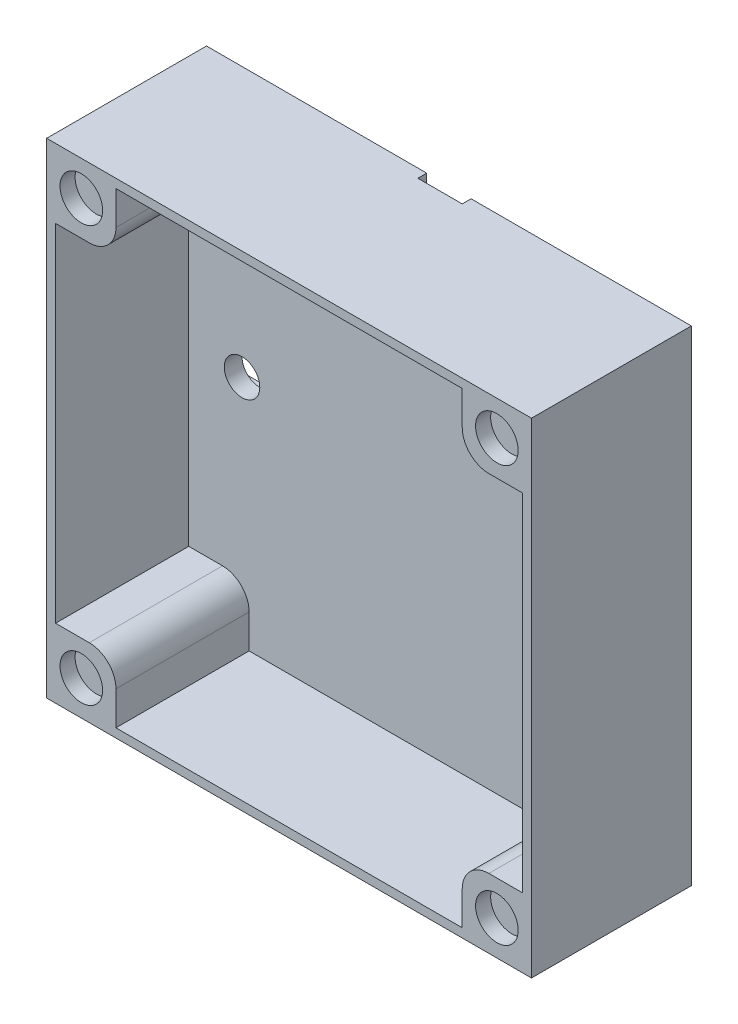
SolidWorks part; units mm, degrees
ref_plane "Přední rovina" through (0, 0, 0) normal (0, 0, 1) x (1, 0, 0)
ref_plane "Horní rovina" through (0, 0, 0) normal (0, 1, 0) x (1, 0, 0)
ref_plane "Pravá rovina" through (0, 0, 0) normal (1, 0, 0) x (0, 0, -1)
sketch "Skica1" plane through (0, 0, 0) normal (0, 0, 1) x (1, 0, 0)
  line L1 (27.3, 27.3) -> (-27.3, 27.3)
  line L2 (27.3, 27.3) -> (27.3, -27.3)
  line L3 (27.3, -27.3) -> (-27.3, -27.3)
  line L4 (-27.3, 27.3) -> (-27.3, -27.3)
  line L5 (27.3, 27.3) -> (-27.3, -27.3) construction
  line L6 (27.3, -27.3) -> (-27.3, 27.3) construction
  point P0 (0, 0)
  point P5 (-27.5, 0)
  point P11 (4.5, 0)
  dimension "D1" = 54.6
  dimension "D2" = 54.6
extrude "Přidat vysunutím2" add sketch "Skica1" along normal blind 3 contours L2 L1 L4 L3
sketch "Skica5" plane through (0, 0, 0) normal (0, 0, -1) x (-1, 0, 0)
  line L0 (-27.3, 27.3) -> (27.3, 27.3) construction
  line L5 (2.5, 27.3) -> (-2.5, 27.3)
  line L15 (27.3, 27.3) -> (27.3, -27.3) construction
  line L16 (-2.5, 2.5) -> (27.3, 2.5)
  line L17 (2.5, 27.3) -> (2.5, 2.5)
  line L18 (2.5, 2.5) -> (-2.5, 2.5)
  line L19 (-2.5, 27.3) -> (-2.5, 2.5)
  line L20 (-27.3, 27.3) -> (-27.3, -27.3) construction
  line L21 (-2.5, 2.5) -> (-2.5, -2.5)
  line L22 (-2.5, -2.5) -> (27.3, -2.5)
  line L23 (27.3, 2.5) -> (27.3, -2.5)
  point P0 (0, 0)
  dimension "D1" = 5
  dimension "D2" = 24.8
  dimension "D3" = 5
  dimension "D4" = 24.8
extrude "Odebrat vysunutím3" cut sketch "Skica5" against normal blind 1 contours L23 L22 L21 L16 | L17 L5 L19 L18
sketch "Skica14" plane through (0, 0, 3) normal (0, 0, 1) x (1, 0, 0)
  line L1 (-27.3, 27.3) -> (27.3, 27.3)
  line L2 (-27.3, 27.3) -> (-27.3, -27.3)
  line L3 (-27.3, -27.3) -> (27.3, -27.3)
  line L4 (27.3, 27.3) -> (27.3, -27.3)
  line L5 (-26.3, 26.3) -> (26.3, 26.3)
  line L6 (-26.3, 26.3) -> (-26.3, -27.3)
  line L7 (-26.3, -27.3) -> (26.3, -27.3)
  line L8 (26.3, 26.3) -> (26.3, -27.3)
  line L9 (-26.3, -27.3) -> (26.3, -27.3)
  line L10 (-26.3, -27.3) -> (-26.3, -26.3)
  line L11 (-26.3, -26.3) -> (26.3, -26.3)
  line L12 (26.3, -27.3) -> (26.3, -26.3)
  line M13 (-27.3, -27.3) -> (27.3, -27.3)
  line M14 (27.3, -27.3) -> (27.3, 27.3)
  line M15 (27.3, 27.3) -> (-27.3, 27.3)
  line M16 (-27.3, 27.3) -> (-27.3, -27.3)
  dimension "D1" = 1
  dimension "D2" = 1
  dimension "D3" = 1
  dimension "D4" = 0
  dimension "D5" = 1
  dimension "D6" = 52.6
extrude "Přidat vysunutím9" add sketch "Skica14" along normal blind 15 contours L5 L8 L6 M13 M14 M15 M16 | L10 L9 L12 L11
sketch "Skica17" plane through (0, 0, 1) normal (0, 0, -1) x (-1, 0, 0)
  line L2 (27.3, 2.5) -> (27.3, -2.5) construction
  line L4 (2.5, 27.3) -> (-2.5, 27.3) construction
  circle A1 centre (20.3, 0) radius 2
  circle A2 centre (0, 20.3) radius 2
  dimension "D2" = 4
  dimension "D6" = 7
  dimension "D4" = 4
  dimension "D5" = 7
extrude "Odebrat vysunutím8" cut sketch "Skica17" against normal blind 7
sketch "Skica19" plane through (0, 0, 0) normal (0, 0, -1) x (-1, 0, 0)
  line L1 (-27.3, 27.3) -> (-19.5, 27.3)
  line L2 (-27.3, 27.3) -> (-27.3, 19.5)
  line L3 (-27.3, 19.5) -> (-19.5, 19.5)
  line L4 (-19.5, 27.3) -> (-19.5, 19.5)
  line L5 (27.3, 27.3) -> (19.5, 27.3)
  line L6 (27.3, 27.3) -> (27.3, 19.5)
  line L7 (27.3, 19.5) -> (19.5, 19.5)
  line L8 (19.5, 27.3) -> (19.5, 19.5)
  line L9 (-27.3, -27.3) -> (-19.5, -27.3)
  line L10 (-27.3, -27.3) -> (-27.3, -19.5)
  line L11 (-27.3, -19.5) -> (-19.5, -19.5)
  line L12 (-19.5, -27.3) -> (-19.5, -19.5)
  line L13 (27.3, -27.3) -> (19.5, -27.3)
  line L14 (27.3, -27.3) -> (27.3, -19.5)
  line L15 (27.3, -19.5) -> (19.5, -19.5)
  line L16 (19.5, -27.3) -> (19.5, -19.5)
  dimension "D1" = 7.8
  dimension "D2" = 7.8
  dimension "D3" = 7.8
  dimension "D4" = 7.8
extrude "Přidat vysunutím10" add sketch "Skica19" against normal blind 18
sketch "Skica20" plane through (0, 0, 18) normal (0, 0, 1) x (1, 0, 0)
  line L0 (-27.3, -27.3) -> (27.3, -27.3) construction
  line L1 (-19.5, -26.3) -> (-19.5, -19.5) construction
  line L2 (-27.3, 27.3) -> (-27.3, -27.3) construction
  line L3 (27.3, 27.3) -> (-27.3, 27.3) construction
  line L4 (27.3, -27.3) -> (27.3, 27.3) construction
  line L5 (-27.3, -27.3) -> (27.3, -27.3) construction
  circle A0 centre (-23.4, -23.4) radius 2.4
  circle A1 centre (-23.4, 23.4) radius 2.4
  circle A2 centre (23.4003, 23.4) radius 2.4
  circle A3 centre (23.4003, -23.4) radius 2.4
  dimension "D1" = 4.8
  dimension "D4" = 4.8
  dimension "D5" = 3.9
  dimension "D7" = 4.8
  dimension "D10" = 4.8
  dimension "D2" = 3.9
  dimension "D3" = 3.9
  dimension "D6" = 3.9
  dimension "D8" = 3.8997
  dimension "D9" = 3.9
  dimension "D11" = 3.9
  dimension "D12" = 3.8997
extrude "Odebrat vysunutím9" cut sketch "Skica20" against normal blind 1.7
fillet "Zaoblit1" radius 3 4 edges at (19.5, 19.5, 10.5) (19.5, -19.5, 10.5) (-19.5, -19.5, 10.5) (-19.5, 19.5, 10.5)
fillet "Zaoblit2" radius 15 1 edges at (-2.5, 2.5, 0.5)
fillet "Zaoblit3" radius 20 1 edges at (2.5, -2.5, 0.5)
